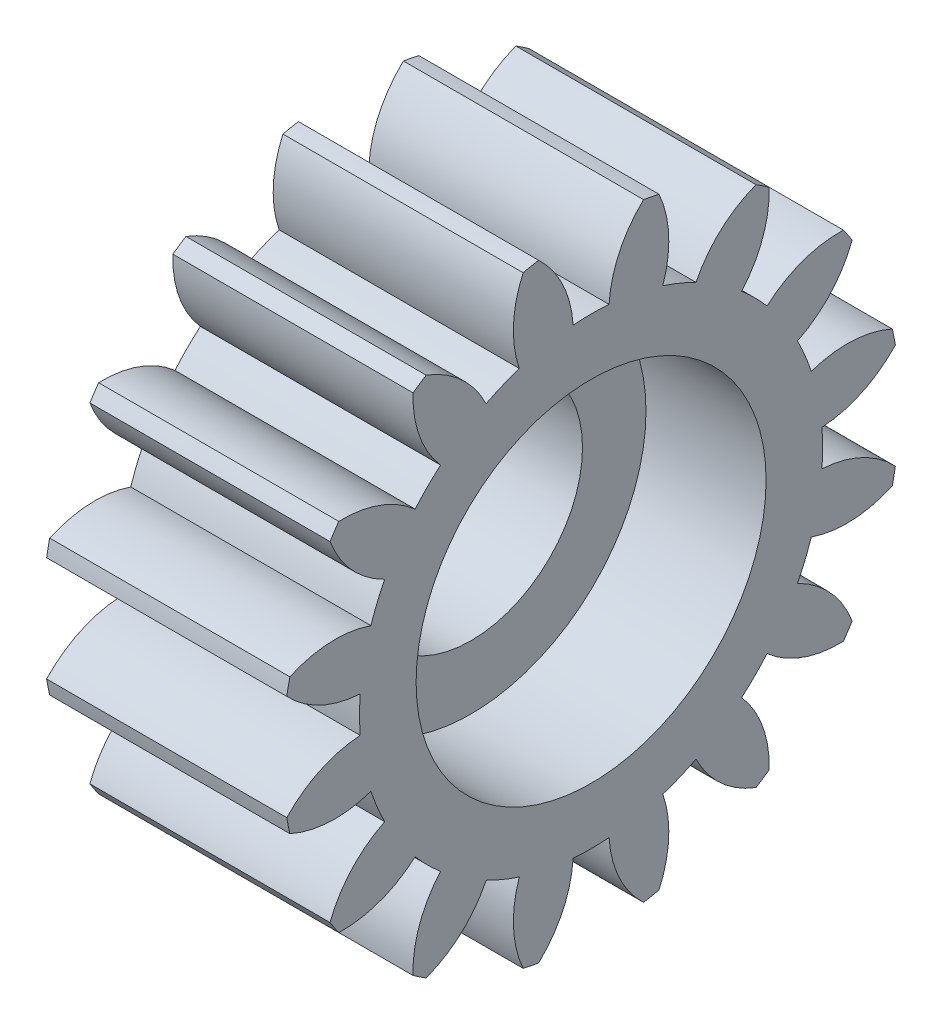
SolidWorks part; units mm, degrees
ref_plane "Plan de face" through (0, 0, 0) normal (0, 0, 1) x (1, 0, 0)
ref_plane "Plan de dessus" through (0, 0, 0) normal (0, 1, 0) x (1, 0, 0)
ref_plane "Plan de droite" through (0, 0, 0) normal (1, 0, 0) x (0, 0, -1)
ref_plane "Plan1" through (7, 0, 0) normal (1, 0, 0) x (0, 0, -1)
sketch "Esquisse1" plane through (7, 0, 0) normal (1, 0, 0) x (0, 0, -1)
  arc A0 (-6.7286, 0.5238) -> (-6.7286, -0.5238) centre (0, 0) ccw
  arc A1 (-6.7286, -0.5238) -> (-8.869, -1.5299) centre (-6.5338, -3.7179) ccw
  arc A2 (-8.869, -1.5299) -> (-8.7794, -1.9805) centre (0, 0) ccw
  arc A3 (-8.7794, -1.9805) -> (-6.4169, -2.091) centre (-7.4592, 0.9345) ccw
  arc A4 (-6.4169, -2.091) -> (-6.016, -3.0589) centre (0, 0) ccw
  arc A5 (-6.016, -3.0589) -> (-7.6084, -4.8075) centre (-4.6137, -5.9352) ccw
  arc A6 (-7.6084, -4.8075) -> (-7.3532, -5.1895) centre (0, 0) ccw
  arc A7 (-7.3532, -5.1895) -> (-5.1282, -4.3875) centre (-7.249, -1.9912) ccw
  arc A8 (-5.1282, -4.3875) -> (-4.3875, -5.1282) centre (0, 0) ccw
  arc A9 (-4.3875, -5.1282) -> (-5.1895, -7.3532) centre (-1.9912, -7.249) ccw
  arc A10 (-5.1895, -7.3532) -> (-4.8075, -7.6084) centre (0, 0) ccw
  arc A11 (-4.8075, -7.6084) -> (-3.0589, -6.016) centre (-5.9352, -4.6137) ccw
  arc A12 (-3.0589, -6.016) -> (-2.091, -6.4169) centre (0, 0) ccw
  arc A13 (-2.091, -6.4169) -> (-1.9805, -8.7794) centre (0.9345, -7.4592) ccw
  arc A14 (-1.9805, -8.7794) -> (-1.5299, -8.869) centre (0, 0) ccw
  arc A15 (-1.5299, -8.869) -> (-0.5238, -6.7286) centre (-3.7179, -6.5338) ccw
  arc A16 (-0.5238, -6.7286) -> (0.5238, -6.7286) centre (0, 0) ccw
  arc A17 (0.5238, -6.7286) -> (1.5299, -8.869) centre (3.7179, -6.5338) ccw
  arc A18 (1.5299, -8.869) -> (1.9805, -8.7794) centre (0, 0) ccw
  arc A19 (1.9805, -8.7794) -> (2.091, -6.4169) centre (-0.9345, -7.4592) ccw
  arc A20 (2.091, -6.4169) -> (3.0589, -6.016) centre (0, 0) ccw
  arc A21 (3.0589, -6.016) -> (4.8075, -7.6084) centre (5.9352, -4.6137) ccw
  arc A22 (4.8075, -7.6084) -> (5.1895, -7.3532) centre (0, 0) ccw
  arc A23 (5.1895, -7.3532) -> (4.3875, -5.1282) centre (1.9912, -7.249) ccw
  arc A24 (4.3875, -5.1282) -> (5.1282, -4.3875) centre (0, 0) ccw
  arc A25 (5.1282, -4.3875) -> (7.3532, -5.1895) centre (7.249, -1.9912) ccw
  arc A26 (7.3532, -5.1895) -> (7.6084, -4.8075) centre (0, 0) ccw
  arc A27 (7.6084, -4.8075) -> (6.016, -3.0589) centre (4.6137, -5.9352) ccw
  arc A28 (6.016, -3.0589) -> (6.4169, -2.091) centre (0, 0) ccw
  arc A29 (6.4169, -2.091) -> (8.7794, -1.9805) centre (7.4592, 0.9345) ccw
  arc A30 (8.7794, -1.9805) -> (8.869, -1.5299) centre (0, 0) ccw
  arc A31 (8.869, -1.5299) -> (6.7286, -0.5238) centre (6.5338, -3.7179) ccw
  arc A32 (6.7286, -0.5238) -> (6.7286, 0.5238) centre (0, 0) ccw
  arc A33 (6.7286, 0.5238) -> (8.869, 1.5299) centre (6.5338, 3.7179) ccw
  arc A34 (8.869, 1.5299) -> (8.7794, 1.9805) centre (0, 0) ccw
  arc A35 (8.7794, 1.9805) -> (6.4169, 2.091) centre (7.4592, -0.9345) ccw
  arc A36 (6.4169, 2.091) -> (6.016, 3.0589) centre (0, 0) ccw
  arc A37 (6.016, 3.0589) -> (7.6084, 4.8075) centre (4.6137, 5.9352) ccw
  arc A38 (7.6084, 4.8075) -> (7.3532, 5.1895) centre (0, 0) ccw
  arc A39 (7.3532, 5.1895) -> (5.1282, 4.3875) centre (7.249, 1.9912) ccw
  arc A40 (5.1282, 4.3875) -> (4.3875, 5.1282) centre (0, 0) ccw
  arc A41 (4.3875, 5.1282) -> (5.1895, 7.3532) centre (1.9912, 7.249) ccw
  arc A42 (5.1895, 7.3532) -> (4.8075, 7.6084) centre (0, 0) ccw
  arc A43 (4.8075, 7.6084) -> (3.0589, 6.016) centre (5.9352, 4.6137) ccw
  arc A44 (3.0589, 6.016) -> (2.091, 6.4169) centre (0, 0) ccw
  arc A45 (2.091, 6.4169) -> (1.9805, 8.7794) centre (-0.9345, 7.4592) ccw
  arc A46 (1.9805, 8.7794) -> (1.5299, 8.869) centre (0, 0) ccw
  arc A47 (1.5299, 8.869) -> (0.5238, 6.7286) centre (3.7179, 6.5338) ccw
  arc A48 (0.5238, 6.7286) -> (-0.5238, 6.7286) centre (0, 0) ccw
  arc A49 (-0.5238, 6.7286) -> (-1.5299, 8.869) centre (-3.7179, 6.5338) ccw
  arc A50 (-1.5299, 8.869) -> (-1.9805, 8.7794) centre (0, 0) ccw
  arc A51 (-1.9805, 8.7794) -> (-2.091, 6.4169) centre (0.9345, 7.4592) ccw
  arc A52 (-2.091, 6.4169) -> (-3.0589, 6.016) centre (0, 0) ccw
  arc A53 (-3.0589, 6.016) -> (-4.8075, 7.6084) centre (-5.9352, 4.6137) ccw
  arc A54 (-4.8075, 7.6084) -> (-5.1895, 7.3532) centre (0, 0) ccw
  arc A55 (-5.1895, 7.3532) -> (-4.3875, 5.1282) centre (-1.9912, 7.249) ccw
  arc A56 (-4.3875, 5.1282) -> (-5.1282, 4.3875) centre (0, 0) ccw
  arc A57 (-5.1282, 4.3875) -> (-7.3532, 5.1895) centre (-7.249, 1.9912) ccw
  arc A58 (-7.3532, 5.1895) -> (-7.6084, 4.8075) centre (0, 0) ccw
  arc A59 (-7.6084, 4.8075) -> (-6.016, 3.0589) centre (-4.6137, 5.9352) ccw
  arc A60 (-6.016, 3.0589) -> (-6.4169, 2.091) centre (0, 0) ccw
  arc A61 (-6.4169, 2.091) -> (-8.7794, 1.9805) centre (-7.4592, -0.9345) ccw
  arc A62 (-8.7794, 1.9805) -> (-8.869, 1.5299) centre (0, 0) ccw
  arc A63 (-8.869, 1.5299) -> (-6.7286, 0.5238) centre (-6.5338, 3.7179) ccw
  circle A64 centre (0, 0) radius 1.5
extrude "Boss.-Extru.1" add sketch "Esquisse1" against normal blind 7
sketch "Esquisse2" plane through (7, 0, 0) normal (1, 0, 0) x (0, 0, -1)
  circle A0 centre (0, 0) radius 5.1
  dimension "D1" = 10.2
extrude "Enlèv. mat.-Extru.1" cut sketch "Esquisse2" against normal blind 3.5
sketch "Esquisse3" plane through (3.5, 0, 0) normal (1, 0, 0) x (0, 0, -1)
  circle A0 centre (0, 0) radius 3.25
  dimension "D1" = 6.5
extrude "Enlèv. mat.-Extru.2" cut sketch "Esquisse3" against normal through all
